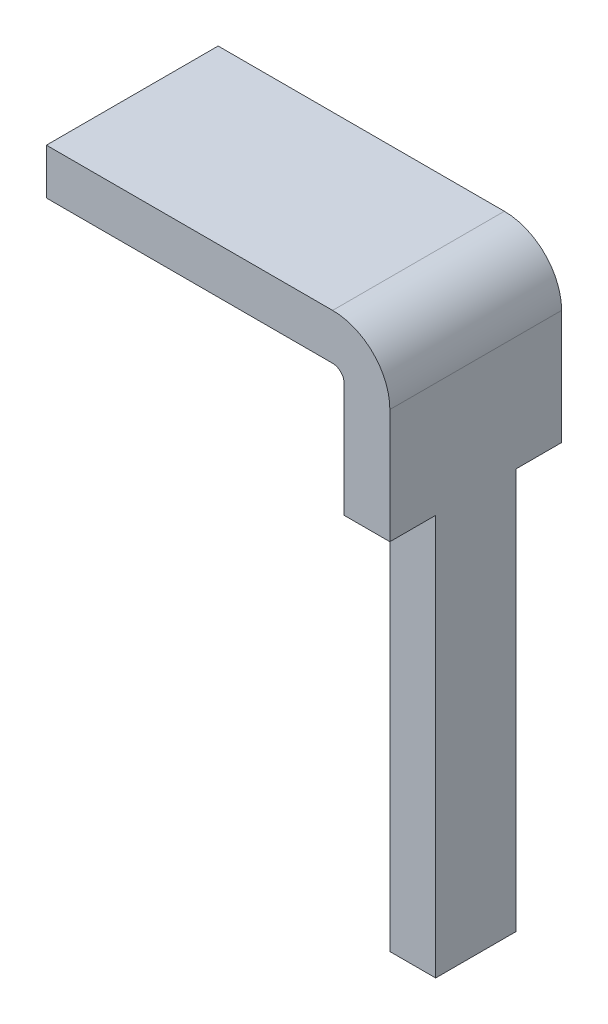
SolidWorks part; units mm, degrees
material "Alloy Steel"
ref_plane "Front Plane" through (0, 0, 0) normal (0, 0, 1) x (1, 0, 0)
ref_plane "Top Plane" through (0, 0, 0) normal (0, 1, 0) x (1, 0, 0)
ref_plane "Right Plane" through (0, 0, 0) normal (1, 0, 0) x (0, 0, -1)
sketch "Sketch1" plane through (0, 0, 0) normal (0, 0, 1) x (1, 0, 0)
  line L0 (0, 0) -> (2.5, 0)
  line L1 (3, -0.5) -> (3, -5)
  line L2 (0, -0.4) -> (2.5, -0.4)
  line L3 (2.6, -0.5) -> (2.6, -5)
  line L4 (0, 0) -> (0, -0.4)
  line L5 (3, -5) -> (2.6, -5)
  arc A0 (2.5, 0) -> (3, -0.5) centre (2.5, -0.5) cw
  arc A1 (2.5, -0.4) -> (2.6, -0.5) centre (2.5, -0.5) cw
  point P6 (3, 0)
  dimension "D3" = 0.5
  dimension "D1" = 3
  dimension "D2" = 5
  dimension "D4" = 0.4
extrude "Boss-Extrude1" add sketch "Sketch1" along normal blind 1.5
sketch "Sketch2" plane through (3, 0, 0) normal (1, 0, 0) x (0, 0, -1)
  line L0 (-0.75, -0.5) -> (-0.75, -5.127) construction
  line L1 (-1.5, -5) -> (-1.1, -5)
  line L2 (-1.5, -5) -> (-1.5, -1.5)
  line L3 (-1.5, -1.5) -> (-1.1, -1.5)
  line L4 (-1.1, -5) -> (-1.1, -1.5)
  line L5 (-1.5, -0.5) -> (0, -0.5) construction
  line L6 (0, -5) -> (-0.4, -5)
  line L7 (0, -5) -> (0, -1.5)
  line L8 (-0.4, -5) -> (-0.4, -1.5)
  line L9 (0, -1.5) -> (-0.4, -1.5)
  dimension "D1" = 3.5
  dimension "D2" = 0.35
extrude "Cut-Extrude1" cut sketch "Sketch2" against normal blind 1.5
